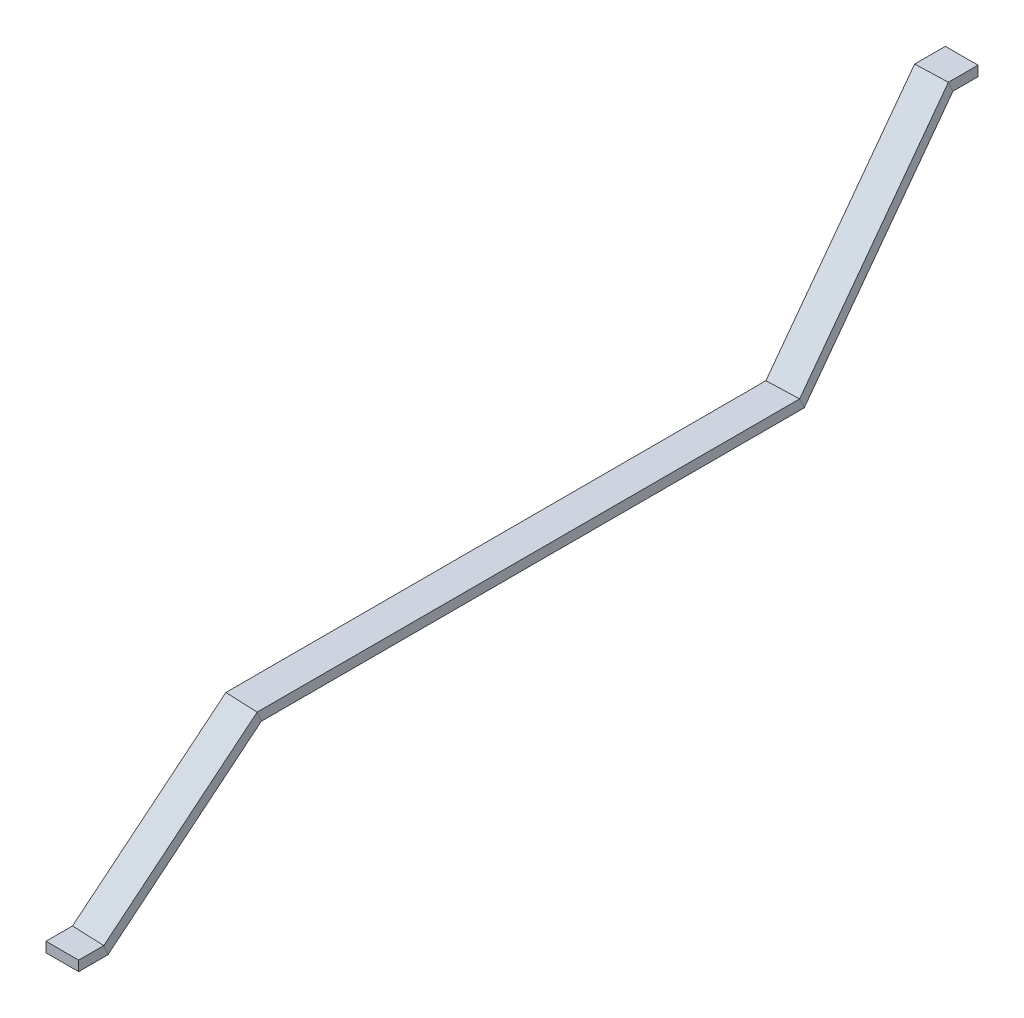
SolidWorks part; units mm, degrees
ref_plane "Front Plane" through (0, 0, 0) normal (0, 0, 1) x (1, 0, 0)
ref_plane "Top Plane" through (0, 0, 0) normal (0, 1, 0) x (1, 0, 0)
ref_plane "Right Plane" through (0, 0, 0) normal (1, 0, 0) x (0, 0, -1)
sketch3d "3DSketch1"
  line L0 (-30, -300, 1465) -> (0, 0, 1165)
  line L1 (0, 0, 1165) -> (0, 0, 0)
  line L2 (0, 0, 0) -> (-30, 400, -350)
  line L3 (-30, 400, -350) -> (-30, 400, -410)
  line L4 (-30, -300, 1465) -> (-30, -300, 1525)
  point P0 (0, 0, 0)
  point P1 (0, 0, 1165)
  point P3 (-30, 400, -350)
  point P4 (-30, 400, -470)
  point P5 (-30, -300, 1465)
  point P6 (-30, -300, 1585)
  dimension "D1" = 1165
  dimension "D2" = 120
  dimension "D3" = 120
  dimension "D4" = 60
  dimension "D5" = 60
ref_plane "Plane1" through (-30, 400, -410) normal (0, 0, 1) x (1, 0, 0)
sketch "Sketch1" plane through (-30, 400, -410) normal (0, 0, 1) x (1, 0, 0)
  line L1 (-35.125, 10.8) -> (35.125, 10.8)
  line L2 (-35.125, 10.8) -> (-35.125, -10.8)
  line L3 (-35.125, -10.8) -> (35.125, -10.8)
  line L4 (35.125, 10.8) -> (35.125, -10.8)
  point P4 (35.125, 0)
  point P5 (0, -10.8)
  dimension "D1" = 70.25
  dimension "D2" = 21.6
sweep "Sweep1" add profiles "Sketch1" path "3DSketch1"
equation "\"strandWidth\"= 21.6"
equation "\"strandHeight\"= 70.25mm"
equation "\"D1@Sketch1\"= \"strandHeight\""
equation "\"D2@Sketch1\"= \"strandWidth\""
equation "\"axialLength\"= 925mm"
equation "\"lengthAfterAxial\"= 240mm"
equation "\"connectionPart\"= 120mm"
equation "\"D1@3DSketch1\"= \"axialLength\"+\"lengthAfterAxial\""
equation "\"D2@3DSketch1\"= \"connectionPart\""
equation "\"D3@3DSketch1\"= \"connectionPart\""
equation "\"D4@3DSketch1\"= \"connectionPart\" / 2"
equation "\"D5@3DSketch1\"= \"connectionPart\" / 2"
